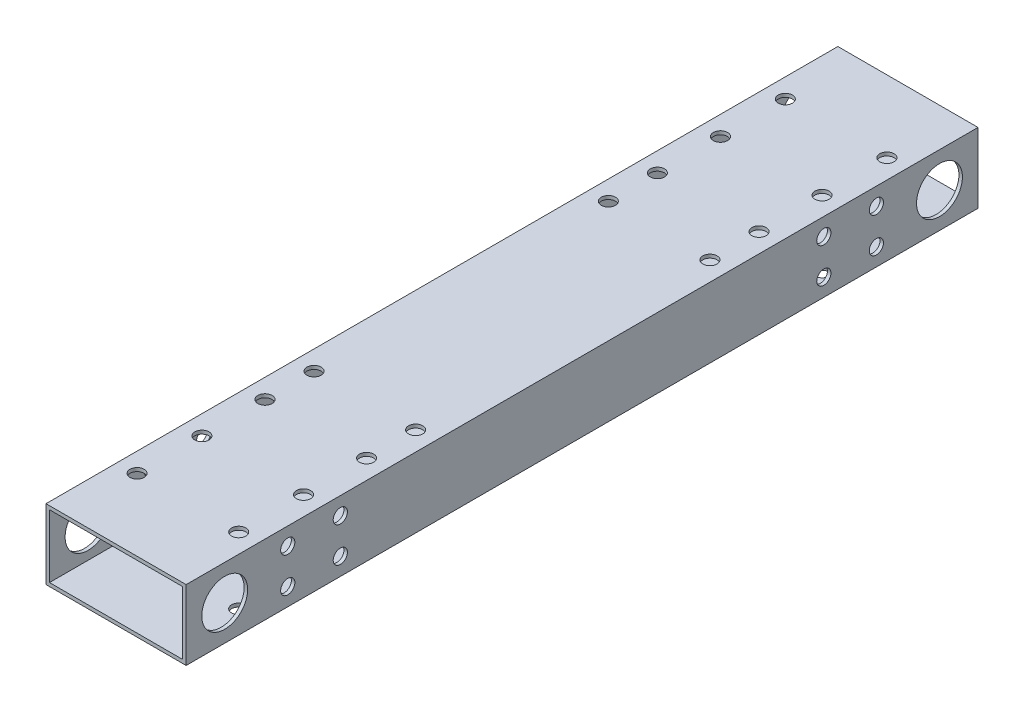
SolidWorks part; units mm, degrees
material "1060 合金"
ref_plane "前视基准面" through (0, 0, 0) normal (0, 0, 1) x (1, 0, 0)
ref_plane "上视基准面" through (0, 0, 0) normal (0, 1, 0) x (1, 0, 0)
ref_plane "右视基准面" through (0, 0, 0) normal (1, 0, 0) x (0, 0, -1)
other "Configuration Table"
sketch "草图1" plane through (0, 0, 0) normal (0, 0, 1) x (1, 0, 0)
  line L0 (-20, -10) -> (-20, 10)
  line L1 (-19, -9) -> (19, -9)
  line L2 (-19, -9) -> (-19, 9)
  line L3 (-19, 9) -> (19, 9)
  line L4 (19, -9) -> (19, 9)
  line L5 (-19, -9) -> (19, 9) construction
  line L6 (-19, 9) -> (19, -9) construction
  line L7 (-20, 10) -> (20, 10)
  line L8 (20, -10) -> (20, 10)
  line L9 (-20, -10) -> (20, -10)
  point P0 (0, 0)
  dimension "D2" = 40
  dimension "D3" = 20
  dimension "D1" = 1
extrude "凸台-拉伸1" add sketch "草图1" along normal mid plane 226
sketch "草图2" plane through (20, 0, 0) normal (1, 0, 0) x (0, 0, -1)
  line L0 (-102, 0) -> (102, 0) construction
  line L1 (113, -10) -> (113, 10) construction
  circle A0 centre (102, 0) radius 6.55
  circle A1 centre (-102, 0) radius 6.55
  point P4 (0, 0)
  dimension "D2" = 13.1
  dimension "D1" = 11
extrude "切除-拉伸1" cut sketch "草图2" against normal blind 40
sketch "草图3" plane through (0, 10, 0) normal (0, 1, 0) x (1, 0, 0)
  line L0 (20, -113) -> (20, 113) construction
  line L1 (-20, 113) -> (20, 113) construction
  line L2 (-20, 113) -> (-20, 83) construction
  line L3 (-20, 83) -> (20, 83) construction
  line L4 (20, 113) -> (20, 83) construction
  line L5 (0, 113) -> (0, 102) construction
  line L6 (0, 102) -> (0, 83) construction
  line L7 (-20, 92.5) -> (20, 92.5) construction
  line L8 (0, 0) -> (50000, 0) construction
  circle A0 centre (-14.5, 92.5) radius 2.025
  circle A1 centre (14.5, 92.5) radius 2.025
  circle A2 centre (14.5, -92.5) radius 2.025
  circle A3 centre (-14.5, -92.5) radius 2.025
  point P14 (0, 92.5)
  dimension "D3" = 4.05
  dimension "D4" = 29
  dimension "D1" = 30
  dimension "D2" = 11
extrude "切除-拉伸2" cut sketch "草图3" against normal blind 30
sketch "草图4" plane through (0, 10, 0) normal (0, 1, 0) x (1, 0, 0)
  line L0 (-14.5, 92.5) -> (14.5, 92.5) construction
  line L1 (0, -92.5) -> (0, 92.5) construction
  line L3 (-14.5, 56) -> (14.5, 56) construction
  line L4 (-14.5, 56) -> (-14.5, 74) construction
  line L5 (-14.5, 74) -> (14.5, 74) construction
  line L6 (14.5, 56) -> (14.5, 74) construction
  line L7 (-14.5, 56) -> (14.5, 74) construction
  line L8 (-14.5, 74) -> (14.5, 56) construction
  line L9 (1.4835, 0) -> (50001.4835, 0) construction
  line L10 (-14.5, -74) -> (14.5, -56) construction
  line L11 (-14.5, -56) -> (14.5, -74) construction
  line L12 (14.5, -56) -> (14.5, -74) construction
  line L13 (-14.5, -74) -> (14.5, -74) construction
  line L14 (-14.5, -56) -> (-14.5, -74) construction
  line L15 (-14.5, -56) -> (14.5, -56) construction
  line L16 (-14.5, -92.5) -> (14.5, -92.5) construction
  circle A0 centre (-14.5, 74) radius 2.025
  circle A1 centre (-14.5, 56) radius 2.025
  circle A2 centre (14.5, 56) radius 2.025
  circle A3 centre (14.5, 74) radius 2.025
  circle A4 centre (14.5, -74) radius 2.025
  circle A5 centre (14.5, -56) radius 2.025
  circle A6 centre (-14.5, -56) radius 2.025
  circle A7 centre (-14.5, -74) radius 2.025
  point P9 (0, 65)
  point P25 (0, 0)
  point P31 (0, -65)
  dimension "D4" = 4.05
  dimension "D1" = 18.5
  dimension "D2" = 18
  dimension "D3" = 29
extrude "切除-拉伸3" cut sketch "草图4" against normal blind 20
sketch "草图6" plane through (0, 10, 0) normal (0, 1, 0) x (1, 0, 0)
  line L1 (-14.5, -42) -> (14.5, -42) construction
  line L2 (-14.5, -42) -> (-14.5, 42) construction
  line L3 (-14.5, 42) -> (14.5, 42) construction
  line L4 (14.5, -42) -> (14.5, 42) construction
  line L5 (-14.5, -42) -> (14.5, 42) construction
  line L6 (-14.5, 42) -> (14.5, -42) construction
  circle A0 centre (-14.5, 42) radius 2.025
  circle A1 centre (14.5, 42) radius 2.025
  circle A2 centre (-14.5, -42) radius 2.025
  circle A3 centre (14.5, -42) radius 2.025
  circle A4 centre (-14.5, 56) radius 2.025 construction
  point P0 (0, 0)
  dimension "D1" = 29
  dimension "D2" = 84
extrude "切除-拉伸4" cut sketch "草图6" against normal blind 30
sketch "草图9" plane through (0, -10, 0) normal (0, -1, 0) x (1, 0, 0)
  line L0 (0, 0) -> (-50000, 0) construction
  circle A0 centre (-14.5, 74) radius 3.75
  circle A1 centre (14.5, 74) radius 3.75
  circle A2 centre (-14.5, 56) radius 3.75
  circle A3 centre (-14.5, 42) radius 3.75
  circle A4 centre (14.5, 42) radius 3.75
  circle A5 centre (14.5, 56) radius 3.75
  circle A6 centre (14.5, -56) radius 3.75
  circle A7 centre (14.5, -42) radius 3.75
  circle A8 centre (-14.5, -42) radius 3.75
  circle A9 centre (-14.5, -56) radius 3.75
  circle A10 centre (14.5, -74) radius 3.75
  circle A11 centre (-14.5, -74) radius 3.75
  dimension "D1" = 7.5
extrude "切除-拉伸5" cut sketch "草图9" against normal blind 2
sketch "草图10" plane through (-20, 0, 0) normal (-1, 0, 0) x (0, 0, 1)
  line L0 (0, 0) -> (50000, 0) construction
  line L2 (84, 5) -> (84, -5) construction
  line L3 (113, 10) -> (113, -10) construction
  line L4 (0, 0) -> (0, -50000) construction
  circle A0 centre (84, 5) radius 2.025
  circle A1 centre (84, -5) radius 2.025
  circle A2 centre (-84, 5) radius 2.025
  circle A3 centre (-84, -5) radius 2.025
  dimension "D1" = 4.05
  dimension "D2" = 10
  dimension "D3" = 29
extrude "切除-拉伸6" cut sketch "草图10" against normal blind 50
sketch "草图11" plane through (0, -10, 0) normal (0, -1, 0) x (1, 0, 0)
  circle A0 centre (14.5, -74) radius 3.75 construction
  circle A1 centre (-14.5, -74) radius 3.75 construction
  circle A2 centre (-14.5, 74) radius 3.75 construction
  circle A3 centre (14.5, 74) radius 3.75 construction
  circle A4 centre (14.5, -74) radius 3.75
  circle A5 centre (-14.5, -74) radius 3.75
  circle A6 centre (-14.5, 74) radius 3.75
  circle A7 centre (14.5, 74) radius 3.75
  circle A8 centre (-14.5, 74) radius 2.025
  circle A9 centre (14.5, 74) radius 2.025
  circle A10 centre (-14.5, -74) radius 2.025
  circle A11 centre (14.5, -74) radius 2.025
  circle A12 centre (14.5, 74) radius 2.025 construction
extrude "凸台-拉伸2" add sketch "草图11" against normal up to surface (1 mm away) up to face at (14.5, -9, 59.75)
sketch "草图13" plane through (20, 0, 0) normal (1, 0, 0) x (0, 0, -1)
  line L0 (0, 0) -> (0, -50000) construction
  line L1 (-84, 5) -> (-69, 5) construction
  line L2 (-84, 5) -> (-84, -5) construction
  line L3 (-84, -5) -> (-69, -5) construction
  line L4 (-69, 5) -> (-69, -5) construction
  line L5 (69, 5) -> (69, -5) construction
  line L6 (84, -5) -> (69, -5) construction
  line L7 (84, 5) -> (84, -5) construction
  line L8 (84, 5) -> (69, 5) construction
  circle A0 centre (-69, 5) radius 2.025
  circle A1 centre (-69, -5) radius 2.025
  circle A2 centre (-84, 5) radius 2.025 construction
  circle A3 centre (69, -5) radius 2.025
  circle A4 centre (69, 5) radius 2.025
  dimension "D1" = 15
extrude "切除-拉伸8" cut sketch "草图13" against normal blind 55
